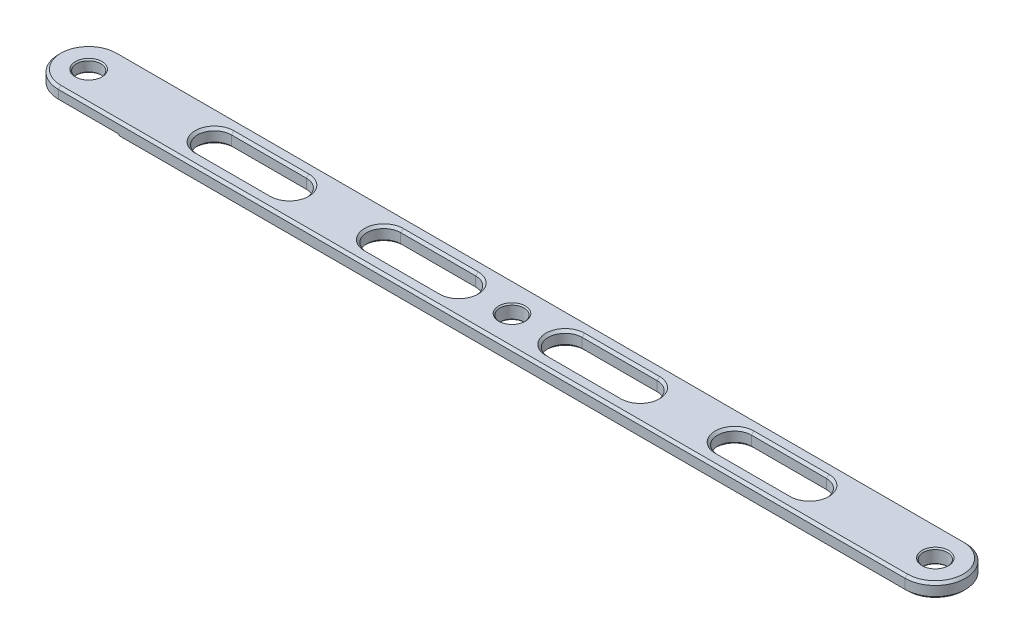
SolidWorks part; units mm, degrees
ref_plane "Plan de face" through (0, 0, 0) normal (0, 0, 1) x (1, 0, 0)
ref_plane "Plan de dessus" through (0, 0, 0) normal (0, 1, 0) x (1, 0, 0)
ref_plane "Plan de droite" through (0, 0, 0) normal (1, 0, 0) x (0, 0, -1)
sketch "Esquisse1" plane through (0, 0, 0) normal (0, 1, 0) x (1, 0, 0)
  line L0 (0, 12.5) -> (350, 12.5)
  line L1 (0, -12.5) -> (350, -12.5)
  line L2 (52, 7) -> (83, 7)
  line L3 (52, -7) -> (83, -7)
  line L4 (0, 0) -> (350, 0) construction
  line L5 (122, 7) -> (153, 7)
  line L6 (153, -7) -> (122, -7)
  line L7 (197, 7) -> (228, 7)
  line L8 (197, -7) -> (228, -7)
  line L9 (267, 7) -> (298, 7)
  line L10 (298, -7) -> (267, -7)
  arc A0 (0, 12.5) -> (0, -12.5) centre (0, 0) ccw
  arc A1 (350, -12.5) -> (350, 12.5) centre (350, 0) ccw
  circle A2 centre (0, 0) radius 5
  circle A3 centre (350, 0) radius 5
  arc A4 (52, 7) -> (52, -7) centre (52, 0) ccw
  arc A5 (83, -7) -> (83, 7) centre (83, 0) ccw
  arc A6 (122, 7) -> (122, -7) centre (122, 0) ccw
  arc A7 (153, -7) -> (153, 7) centre (153, 0) ccw
  arc A8 (197, 7) -> (197, -7) centre (197, 0) ccw
  arc A9 (228, -7) -> (228, 7) centre (228, 0) ccw
  arc A10 (267, 7) -> (267, -7) centre (267, 0) ccw
  arc A11 (298, -7) -> (298, 7) centre (298, 0) ccw
  circle A12 centre (175, 0) radius 5
  dimension "D1" = 25
  dimension "D4" = 10
  dimension "D5" = 45
  dimension "D6" = 45
  dimension "D7" = 10
  dimension "D11" = 45
  dimension "D8" = 25
  dimension "D17" = 10
  dimension "D2" = 14
  dimension "D3" = 350
  dimension "D9" = 14
  dimension "D10" = 14
  dimension "D12" = 45
  dimension "D13" = 14
  dimension "D14" = 45
  dimension "D15" = 25
  dimension "D16" = 45
  dimension "D18" = 175
extrude "Boss.-Extru.1" add sketch "Esquisse1" along normal blind 6
sketch "Esquisse2" plane through (0, 0, 0) normal (0, -1, 0) x (1, 0, 0)
  line L0 (0, -12.5) -> (25, -12.5)
  line L1 (350, -12.5) -> (0, -12.5) construction
  line L2 (25, -12.5) -> (25, 12.5)
  line L3 (0, 12.5) -> (350, 12.5) construction
  line L4 (25, 12.5) -> (0, 12.5)
  arc A0 (0, 12.5) -> (0, -12.5) centre (0, 0) ccw
  circle A1 centre (0, 0) radius 5
  circle A2 centre (0, 0) radius 5 construction
  dimension "D1" = 37.5
extrude "Enlèv. mat.-Extru.1" cut sketch "Esquisse2" against normal blind 1
chamfer "Chanfrein7" distance 0.5 angle 45 3 edges at (12.5, 1, 12.5) (-12.5, 1, 0) (12.5, 1, -12.5)
chamfer "Chanfrein8" distance 1 angle 45 32 edges at (67.5, 6, -7) (45, 6, 0) (90, 6, 0) (67.5, 6, 7) (137.5, 6, -7) (115, 6, 0) (160, 6, 0) (137.5, 6, 7) (212.5, 6, -7) (190, 6, 0) (235, 6, 0) (212.5, 6, 7) (282.5, 6, -7) (260, 6, 0) (305, 6, 0) (282.5, 6, 7) (282.5, 0, -7) (260, 0, 0) (305, 0, 0) (282.5, 0, 7) (212.5, 0, -7) (190, 0, 0) (235, 0, 0) (212.5, 0, 7) (137.5, 0, -7) (115, 0, 0) (160, 0, 0) (137.5, 0, 7) (67.5, 0, -7) (45, 0, 0) (90, 0, 0) (67.5, 0, 7)
chamfer "Chanfrein9" distance 1 angle 45 3 edges at (187.5, 0, 12.5) (362.5, 0, 0) (187.5, 0, -12.5)
chamfer "Chanfrein10" distance 1 angle 45 4 edges at (175, 6, 12.5) (362.5, 6, 0) (-12.5, 6, 0) (175, 6, -12.5)
chamfer "Chanfrein11" distance 0.5 angle 45 2 edges at (175, 0, 5) (175, 6, 5)
chamfer "Chanfrein12" distance 0.5 angle 45 4 edges at (0, 1, -5) (0, 6, 5) (350, 0, 5) (350, 6, 5)
